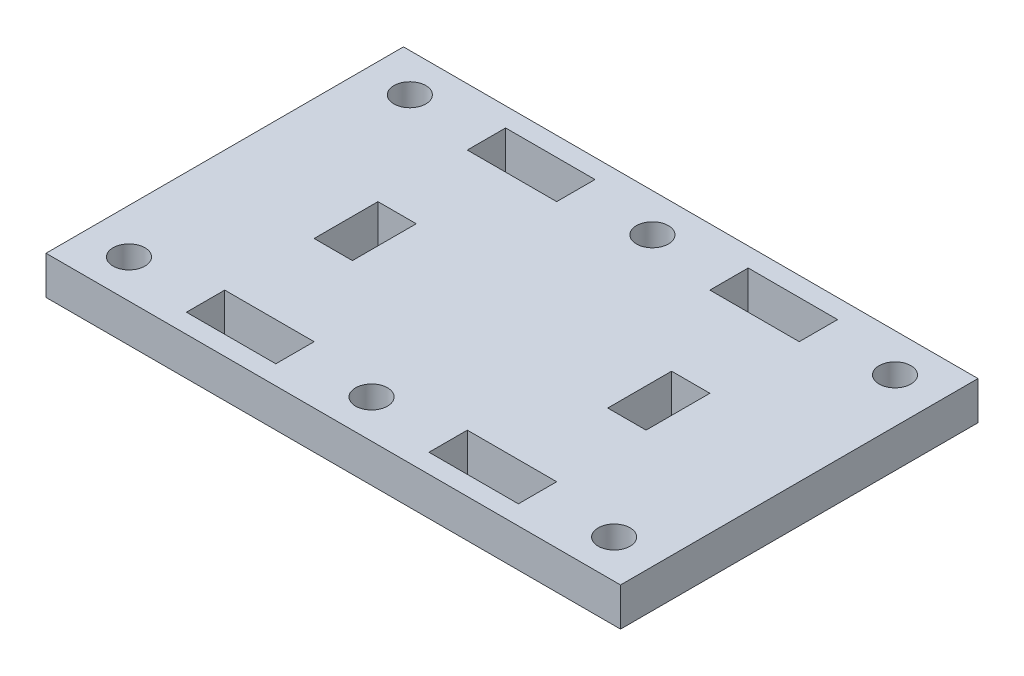
SolidWorks part; units mm, degrees
ref_plane "정면" through (0, 0, 0) normal (0, 0, 1) x (1, 0, 0)
ref_plane "윗면" through (0, 0, 0) normal (0, 1, 0) x (1, 0, 0)
ref_plane "우측면" through (0, 0, 0) normal (1, 0, 0) x (0, 0, -1)
sketch "스케치1" plane through (0, 0, 0) normal (0, 1, 0) x (1, 0, 0)
  line L1 (0, 0) -> (45, 0)
  line L2 (0, 0) -> (0, 28)
  line L3 (0, 28) -> (45, 28)
  line L4 (45, 0) -> (45, 28)
  dimension "D1" = 28
  dimension "D2" = 45
extrude "보스-돌출1" add sketch "스케치1" along normal blind 3
sketch "스케치2" plane through (0, 3, 0) normal (0, 1, 0) x (1, 0, 0)
  line L0 (0, 28) -> (0, 0) construction
  line L1 (-9.4122, 14) -> (48.0652, 14) construction
  line L2 (22.5, 30.6218) -> (22.5, -1.6898) construction
  line L3 (0, 0) -> (45, 0) construction
  line L8 (35.5, 1.5) -> (28.5, 1.5)
  line L9 (28.5, 4.5) -> (28.5, 1.5)
  line L10 (9.5, 4.5) -> (16.5, 4.5)
  line L11 (9.5, 4.5) -> (9.5, 1.5)
  line L12 (9.5, 1.5) -> (16.5, 1.5)
  line L13 (16.5, 4.5) -> (16.5, 1.5)
  line L14 (35.5, 4.5) -> (28.5, 4.5)
  line L15 (35.5, 4.5) -> (35.5, 1.5)
  line L16 (35.5, 23.5) -> (35.5, 26.5)
  line L17 (35.5, 23.5) -> (28.5, 23.5)
  line L18 (28.5, 23.5) -> (28.5, 26.5)
  line L19 (35.5, 26.5) -> (28.5, 26.5)
  line L20 (9.5, 26.5) -> (16.5, 26.5)
  line L21 (16.5, 23.5) -> (16.5, 26.5)
  line L22 (9.5, 23.5) -> (16.5, 23.5)
  line L23 (9.5, 23.5) -> (9.5, 26.5)
  circle A0 centre (22.5, 3) radius 1.25
  circle A1 centre (22.5, 25) radius 1.25
  circle A2 centre (3.5, 3) radius 1.25
  circle A3 centre (41.5, 3) radius 1.25
  circle A4 centre (41.5, 25) radius 1.25
  circle A5 centre (3.5, 25) radius 1.25
  point P0 (0, 3)
  point P1 (0, 14)
  point P12 (3.5, 0)
  dimension "D2" = 2.5
  dimension "D4" = 2.5
  dimension "D5" = 22.5
  dimension "D1" = 11
  dimension "D3" = 19
  dimension "D6" = 19
  dimension "D7" = 1.5
  dimension "D8" = 3
  dimension "D9" = 7
  dimension "D10" = 6
extrude "컷-돌출1" cut sketch "스케치2" against normal through all
sketch "스케치3" plane through (0, 3, 0) normal (0, 1, 0) x (1, 0, 0)
  line L1 (9.5, 11.5) -> (12.5, 11.5)
  line L2 (9.5, 11.5) -> (9.5, 16.5)
  line L3 (9.5, 16.5) -> (12.5, 16.5)
  line L4 (12.5, 11.5) -> (12.5, 16.5)
  line L5 (9.5, 26.5) -> (9.5, 23.5) construction
  line L6 (22.5, -5.8736) -> (22.5, 33.7013) construction
  line L7 (35.5, 16.5) -> (32.5, 16.5)
  line L8 (32.5, 11.5) -> (32.5, 16.5)
  line L9 (35.5, 11.5) -> (32.5, 11.5)
  line L10 (35.5, 11.5) -> (35.5, 16.5)
  dimension "D1" = 5
  dimension "D2" = 11.5
  dimension "D3" = 3
extrude "컷-돌출2" cut sketch "스케치3" against normal through all
